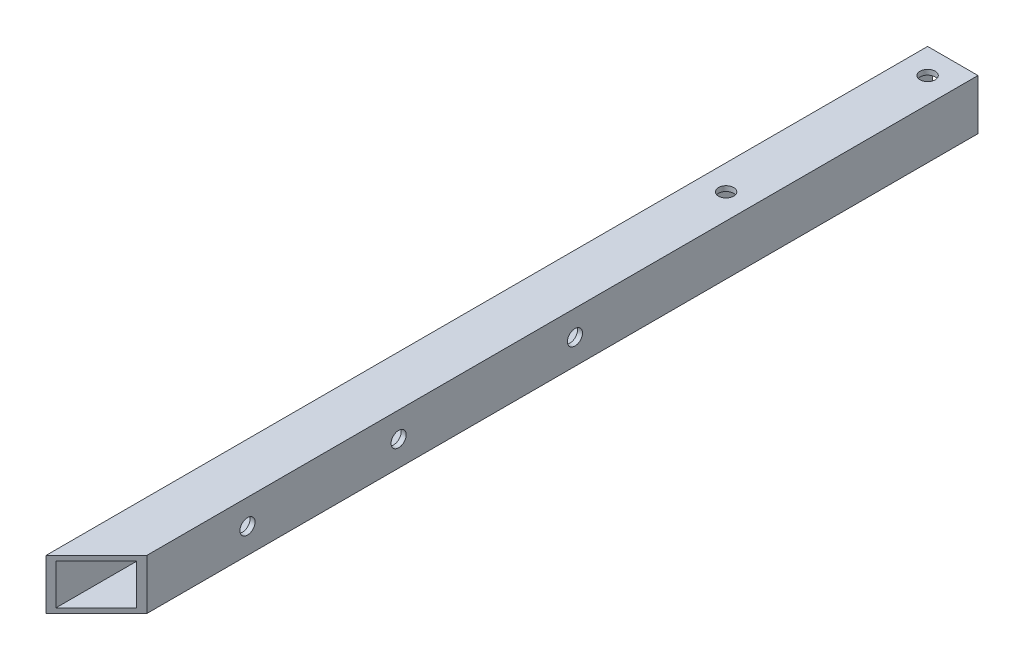
SolidWorks part; units mm, degrees
material "6063-O"
ref_plane "前视基准面" through (0, 0, 0) normal (0, 0, 1) x (1, 0, 0)
ref_plane "上视基准面" through (0, 0, 0) normal (0, 1, 0) x (1, 0, 0)
ref_plane "右视基准面" through (0, 0, 0) normal (1, 0, 0) x (0, 0, -1)
other "Configuration Table"
sketch "草图1" plane through (0, 0, 0) normal (0, 0, 1) x (1, 0, 0)
  line L1 (-5, 5) -> (5, 5)
  line L2 (-5, 5) -> (-5, -5)
  line L3 (-5, -5) -> (5, -5)
  line L4 (5, 5) -> (5, -5)
  line L5 (-5, 5) -> (5, -5) construction
  line L6 (-5, -5) -> (5, 5) construction
  point P4 (0, 0)
  dimension "D1" = 10
  dimension "D2" = 10
extrude "拉伸-薄壁1" add sketch "草图1" along normal blind 175 thin
sketch "草图2" plane through (5, 0, 0) normal (1, 0, 0) x (0, 0, -1)
  line L0 (0, 0) -> (-5, 0) construction
  line L1 (0, -5) -> (0, 5) construction
  line L2 (-5, 0) -> (-175, 0) construction
  line L3 (-175, -5) -> (-175, 5) construction
  circle A0 centre (-5, 0) radius 1.5 construction
  circle A1 centre (-80, 0) radius 1.5
  circle A2 centre (-115, 0) radius 1.5
  circle A3 centre (-145, 0) radius 1.5
  dimension "D2" = 3
  dimension "D3" = 75
  dimension "D4" = 35
  dimension "D5" = 30
  dimension "D1" = 5
extrude "切除-拉伸1" cut sketch "草图2" against normal through all
sketch "草图3" plane through (0, 5, 0) normal (0, 1, 0) x (1, 0, 0)
  line L0 (0, 0) -> (0, -175) construction
  line L1 (5, 0) -> (-5, 0) construction
  line L4 (5, -175) -> (5, 0) construction
  line L5 (5, -165) -> (5, -175)
  line L8 (5, -175) -> (-5, -175) construction
  line L9 (-5, -175) -> (5, -175)
  line L10 (-5, -175) -> (-5, 0) construction
  line L11 (-5, -175) -> (5, -165)
  circle A0 centre (0, -5) radius 1.5
  circle A1 centre (0, -45) radius 1.5
  dimension "D1" = 3
  dimension "D2" = 5
  dimension "D3" = 40
  dimension "D4" = 45
extrude "切除-拉伸2" cut sketch "草图3" against normal blind 10
